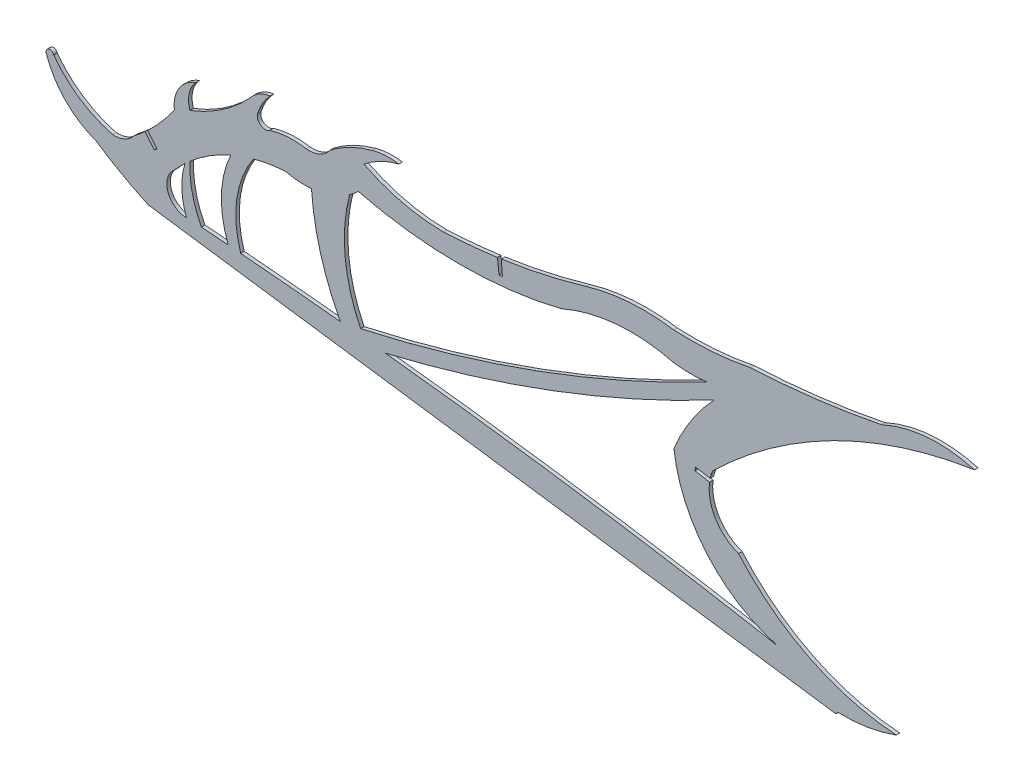
SolidWorks part; units mm, degrees
ref_plane "Front Plane" through (0, 0, 0) normal (0, 0, 1) x (1, 0, 0)
ref_plane "Top Plane" through (0, 0, 0) normal (0, 1, 0) x (1, 0, 0)
ref_plane "Right Plane" through (0, 0, 0) normal (1, 0, 0) x (0, 0, -1)
sketch "Sketch1" plane through (0, 0, 0) normal (0, 0, 1) x (1, 0, 0)
  line L2 (57.2908, 228.1083) -> (353.7115, 186.322)
  arc A0 (328.4892, 199.1824) -> (159.5783, 223.8671) centre (-104.2022, -2171.3607) ccw
  arc A1 (73.8894, 231.5214) -> (68.6319, 246.6774) centre (73.8894, 240.0113) cw
  arc A2 (68.6319, 246.6774) -> (73.1908, 251.4089) centre (120.7421, 201.0308) cw
  arc A3 (116.5511, 270.1793) -> (127.7241, 269.3121) centre (124.7166, 302.9744) ccw
  arc A4 (147.8544, 278.3404) -> (235.3903, 278.3404) centre (191.6224, 455.7178) ccw
  arc A5 (235.3903, 278.3404) -> (283.8697, 282.4058) centre (265.4708, 210.7226) cw
  arc A6 (283.8697, 282.4058) -> (297.9362, 282.3661) centre (291.0514, 334.9586) ccw
  arc A7 (301.1311, 277.1595) -> (283.8697, 250.4336) centre (366.5651, 215.9606) ccw
  arc A8 (328.4892, 199.1824) -> (283.8697, 250.4336) centre (344.1075, 257.8283) cw
  arc A9 (144.1663, 275.3356) -> (148.8842, 227.6654) centre (210.2297, 257.8053) ccw
  arc A10 (127.7241, 269.3121) -> (140.1872, 225.9233) centre (235.7549, 276.8587) ccw
  arc A11 (102.7862, 267.9387) -> (97.2408, 229.9134) centre (138.4351, 243.3229) ccw
  arc A12 (92.9631, 264.4927) -> (91.8733, 230.3576) centre (132.143, 246.1568) ccw
  arc A13 (75.3557, 253.3677) -> (80.3107, 231.2736) centre (118.3573, 251.4089) ccw
  arc A14 (73.1908, 251.4089) -> (73.8894, 231.5214) centre (102.254, 242.4738) ccw
  arc A15 (75.3557, 253.3677) -> (92.9631, 264.4927) centre (120.7421, 201.0308) cw
  arc A16 (102.7862, 267.9387) -> (116.5511, 270.1793) centre (120.7421, 201.0308) cw
  arc A17 (91.8733, 230.3576) -> (80.3107, 231.2736) centre (-104.2022, -2171.3607) ccw
  arc A18 (140.1872, 225.9233) -> (97.2408, 229.9134) centre (-104.2022, -2171.3607) ccw
  arc A19 (144.1663, 275.3356) -> (147.8544, 278.3404) centre (124.7166, 302.9744) ccw
  arc A21 (297.9362, 282.3661) -> (148.8842, 227.6654) centre (20.479, 807.976) cw
  arc A22 (301.1311, 277.1595) -> (159.5783, 223.8671) centre (20.479, 807.976) cw
  arc A58 (34.9897, 240.6666) -> (57.2908, 228.1083) centre (124.6256, 373.7624) ccw
  arc A59 (353.7115, 186.322) -> (354.4333, 187.2865) centre (319.8251, 212.434) ccw
  arc A60 (354.4333, 187.2865) -> (379.7362, 191.4119) centre (356.4501, 254.5755) ccw
  arc A61 (311.7555, 225.1575) -> (379.7362, 191.4119) centre (386.3361, 290.0542) ccw
  arc A62 (300.5625, 250.4336) -> (311.7555, 225.1575) centre (318.0025, 243.0402) ccw
  arc A63 (343.5995, 282.8928) -> (300.5625, 250.4336) centre (448.6234, 98.8832) ccw
  arc A64 (413.3877, 307.235) -> (343.5995, 282.8928) centre (444.2474, 106.5502) ccw
  arc A65 (413.3877, 307.235) -> (373.3389, 304.0502) centre (397.6657, 251.5406) ccw
  arc A66 (316.7305, 297.0926) -> (373.3389, 304.0502) centre (298.5777, 678.5526) ccw
  arc A67 (283.8697, 294.6521) -> (316.7305, 297.0926) centre (290.7187, 424.8879) ccw
  arc A68 (283.8697, 294.6521) -> (246.0954, 292.0212) centre (270.8801, 208.6617) ccw
  arc A69 (184.6162, 281.5894) -> (246.0954, 292.0212) centre (172.4306, 539.7815) ccw
  arc A70 (150.3405, 289.7385) -> (184.6162, 281.5894) centre (184.7892, 358.4744) ccw
  arc A71 (165.4063, 297.3313) -> (150.3405, 289.7385) centre (174.096, 261.3457) ccw
  arc A72 (165.4063, 297.3313) -> (153.9595, 296.712) centre (161.1352, 270.1793) ccw
  arc A73 (153.9595, 296.712) -> (135.7697, 287.7262) centre (167.6472, 246.1006) ccw
  arc A74 (125.5196, 283.0817) -> (135.7697, 287.7262) centre (126.7443, 294.0116) ccw
  arc A75 (125.5196, 283.0817) -> (109.7471, 282.1054) centre (119.6632, 249.7989) ccw
  arc A76 (104.4417, 285.5283) -> (109.7471, 282.1054) centre (107.7252, 284.7946) ccw
  arc A77 (109.9211, 294.9774) -> (104.4417, 285.5283) centre (127.7241, 278.3404) ccw
  arc A78 (109.9211, 294.9774) -> (101.5754, 290.3041) centre (111.5891, 282.21) ccw
  arc A79 (75.3557, 272.3016) -> (101.5754, 290.3041) centre (50.6742, 336.3439) ccw
  arc A80 (77.9793, 284.0254) -> (75.3557, 272.3016) centre (86.3085, 276.0059) ccw
  arc A81 (77.9793, 284.0254) -> (68.6319, 269.199) centre (82.4264, 270.8619) ccw
  arc A82 (51.3192, 250.8509) -> (68.6319, 269.199) centre (3.2114, 313.5861) ccw
  arc A83 (42.0381, 246.6774) -> (51.3192, 250.8509) centre (42.7992, 257.3914) ccw
  arc A84 (16.6466, 263.6546) -> (42.0381, 246.6774) centre (53.2769, 290.963) ccw
  arc A85 (16.6466, 263.6546) -> (13.4695, 262.5682) centre (15.0185, 263.2273) ccw
  arc A86 (13.4695, 262.5682) -> (34.9897, 240.6666) centre (47.067, 274.057) ccw
extrude "Boss-Extrude1" add sketch "Sketch1" along normal blind 1.524
sketch "Sketch2" plane through (0, 0, 0) normal (0, 0, -1) x (-1, 0, 0)
  line L0 (-290.2269, 248.7218) -> (-289.9618, 247.2211) construction
  line L1 (-293.2284, 248.1915) -> (-292.9633, 246.6907)
  line L2 (-292.9633, 246.6907) -> (-301.8316, 245.1237)
  line L3 (-301.8316, 245.1237) -> (-302.0967, 246.6245)
  line L4 (-302.0967, 246.6245) -> (-293.2284, 248.1915)
  line L5 (-210.335, 274.5797) -> (-208.8609, 274.4221) construction
  line L6 (-210.011, 277.6104) -> (-208.537, 277.4529)
  line L7 (-208.537, 277.4529) -> (-207.7251, 285.0477)
  line L8 (-207.7251, 285.0477) -> (-209.3843, 285.2022)
  line L9 (-209.3843, 285.2022) -> (-210.011, 277.6104)
  line L10 (-63.1143, 248.4625) -> (-61.9316, 247.5013) construction
  line L11 (-61.1919, 250.8278) -> (-60.0092, 249.8666)
  line L12 (-60.0092, 249.8666) -> (-54.9398, 256.1042)
  line L13 (-54.9398, 256.1042) -> (-56.2085, 256.9596)
  line L14 (-56.2085, 256.9596) -> (-61.1919, 250.8278)
  dimension "D1" = 3.048
  dimension "D2" = 3.048
  dimension "D3" = 3.048
extrude "Cut-Extrude1" cut sketch "Sketch2" against normal blind 1.524
